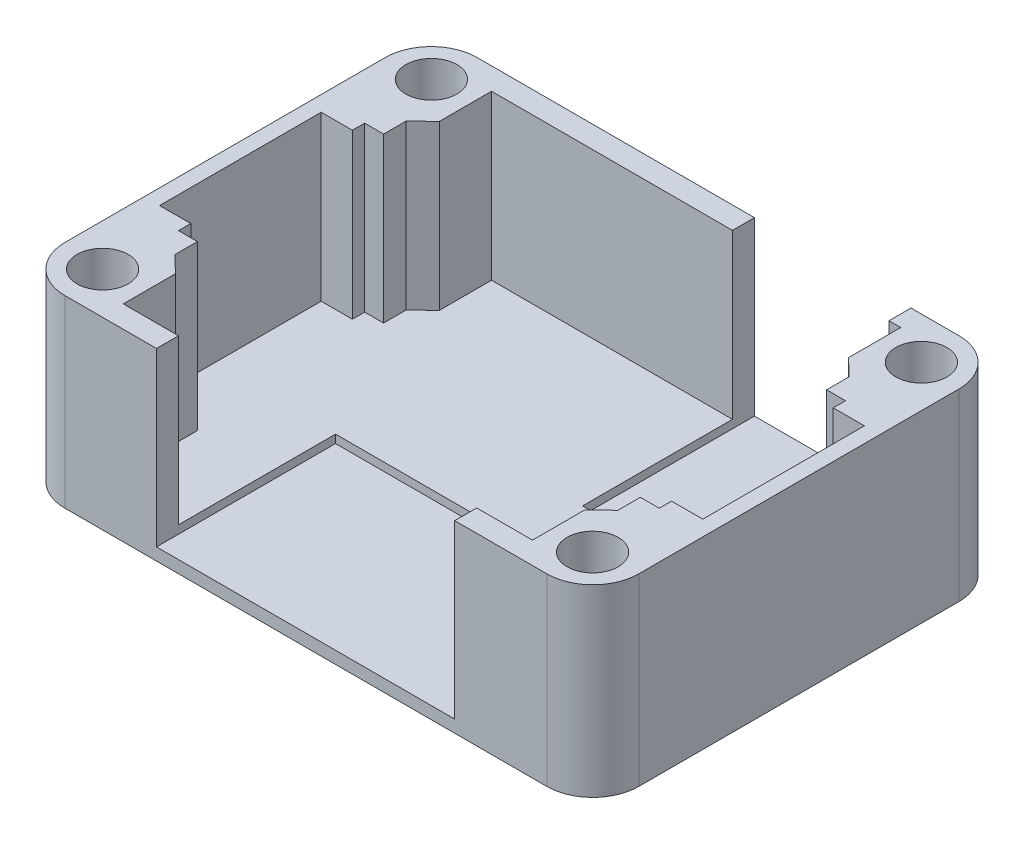
SolidWorks part; units mm, degrees
ref_plane "Front Plane" through (0, 0, 0) normal (0, 0, 1) x (1, 0, 0)
ref_plane "Top Plane" through (0, 0, 0) normal (0, 1, 0) x (1, 0, 0)
ref_plane "Right Plane" through (0, 0, 0) normal (1, 0, 0) x (0, 0, -1)
sketch "Sketch1" plane through (0, 0, 0) normal (0, 1, 0) x (1, 0, 0)
  line L1 (-20, -18) -> (20, -18)
  line L3 (-20, 18) -> (20, 18)
  line L5 (-20, -18) -> (20, 18) construction
  line L6 (-20, 18) -> (20, -18) construction
  line L9 (-20, -12.9) -> (-21.65, -11.3)
  line L16 (-20, -18) -> (-20, -12.9)
  line L17 (-21.65, -11.3) -> (-21.65, -9.1)
  line L18 (-21.65, -9.1) -> (-23.5, -9.1)
  line L19 (-23.5, -9.1) -> (-23.5, -7.9)
  line L20 (-23.5, -7.9) -> (-26.55, -7.9)
  line L21 (-26.55, -7.9) -> (-26.55, 7.9)
  line L22 (-55, 0) -> (55, 0) construction
  line L23 (-23.5, 7.9) -> (-26.55, 7.9)
  line L24 (-23.5, 9.1) -> (-23.5, 7.9)
  line L25 (-21.65, 9.1) -> (-23.5, 9.1)
  line L26 (-21.65, 11.3) -> (-21.65, 9.1)
  line L27 (-20, 12.9) -> (-21.65, 11.3)
  line L28 (-20, 18) -> (-20, 12.9)
  line L29 (0, -55) -> (0, 55) construction
  line L30 (20, 18) -> (20, 12.9)
  line L31 (20, 12.9) -> (21.65, 11.3)
  line L32 (21.65, 11.3) -> (21.65, 9.1)
  line L33 (21.65, 9.1) -> (23.5, 9.1)
  line L34 (23.5, 9.1) -> (23.5, 7.9)
  line L35 (23.5, 7.9) -> (26.55, 7.9)
  line L36 (26.55, -7.9) -> (26.55, 7.9)
  line L37 (23.5, -7.9) -> (26.55, -7.9)
  line L38 (23.5, -9.1) -> (23.5, -7.9)
  line L39 (21.65, -9.1) -> (23.5, -9.1)
  line L40 (21.65, -11.3) -> (21.65, -9.1)
  line L41 (20, -18) -> (20, -12.9)
  line L42 (20, -12.9) -> (21.65, -11.3)
  line L43 (0, 28.0577) -> (0, -22.6884) construction
  line L44 (23.55, 20.15) -> (-23.55, 20.15)
  line L45 (28.05, 15.65) -> (28.05, -15.65)
  line L46 (23.55, -20.15) -> (-23.55, -20.15)
  line L47 (-28.05, 15.65) -> (-28.05, -15.65)
  line L48 (28.05, 20.15) -> (-28.05, -20.15) construction
  line L49 (28.05, -20.15) -> (-28.05, 20.15) construction
  arc A0 (-23.55, 20.15) -> (-28.05, 15.65) centre (-23.55, 15.65) ccw
  arc A1 (23.55, 20.15) -> (28.05, 15.65) centre (23.55, 15.65) cw
  arc A2 (28.05, -15.65) -> (23.55, -20.15) centre (23.55, -15.65) cw
  arc A3 (-23.55, -20.15) -> (-28.05, -15.65) centre (-23.55, -15.65) cw
  point P0 (0, 0)
  point P10 (0, 0)
  point P17 (-26.55, 0)
  point P36 (25.8, 0)
  point P53 (0, 0)
  point P54 (0, 0)
  point P55 (0, 28.0577)
  point P56 (0, 0)
  dimension "D12" = 4.5
  dimension "D1" = 5.1
  dimension "D2" = 40
  dimension "D3" = 36
  dimension "D4" = 15.8
  dimension "D5" = 18.2
  dimension "D6" = 22.6
  dimension "D7" = 1.5
  dimension "D8" = 47
  dimension "D9" = 43.3
  dimension "D10" = 56.1
  dimension "D11" = 40.3
  dimension "D13" = 1.5
extrude "Boss-Extrude1" add sketch "Sketch1" along normal blind 16
sketch "Sketch2" plane through (0, 0, 0) normal (0, -1, 0) x (1, 0, 0)
  line L4 (-23.55, -20.15) -> (23.55, -20.15)
  line L5 (28.05, -15.65) -> (28.05, 15.65)
  line L6 (23.55, 20.15) -> (-23.55, 20.15)
  line L7 (-28.05, 15.65) -> (-28.05, -15.65)
  line L8 (-23.55, -20.15) -> (23.55, -20.15)
  line L9 (28.05, -15.65) -> (28.05, 15.65)
  line L10 (23.55, 20.15) -> (-23.55, 20.15)
  line L11 (-28.05, 15.65) -> (-28.05, -15.65)
  arc A4 (-28.05, -15.65) -> (-23.55, -20.15) centre (-23.55, -15.65) ccw
  arc A5 (23.55, -20.15) -> (28.05, -15.65) centre (23.55, -15.65) ccw
  arc A6 (28.05, 15.65) -> (23.55, 20.15) centre (23.55, 15.65) ccw
  arc A7 (-23.55, 20.15) -> (-28.05, 15.65) centre (-23.55, 15.65) ccw
  arc A8 (-28.05, -15.65) -> (-23.55, -20.15) centre (-23.55, -15.65) ccw
  arc A9 (23.55, -20.15) -> (28.05, -15.65) centre (23.55, -15.65) ccw
  arc A10 (28.05, 15.65) -> (23.55, 20.15) centre (23.55, 15.65) ccw
  arc A11 (-23.55, 20.15) -> (-28.05, 15.65) centre (-23.55, 15.65) ccw
  dimension "D1" = 0
extrude "Boss-Extrude2" add sketch "Sketch2" along normal blind 2
sketch "Sketch3" plane through (0, 0, -20.15) normal (0, 0, -1) x (-1, 0, 0)
  line L0 (-23.55, 16) -> (23.55, 16) construction
  line L1 (-18.85, 16) -> (-3.55, 16)
  line L2 (-18.85, 16) -> (-18.85, -0.8)
  line L3 (-18.85, -0.8) -> (-3.55, -0.8)
  line L4 (-3.55, 16) -> (-3.55, -0.8)
  line L6 (28.05, 16) -> (28.05, -2) construction
  point P11 (-4.6086, 20)
  dimension "D1" = 31.6
  dimension "D2" = 15.3
  dimension "D3" = 16.8
extrude "Cut-Extrude1" cut sketch "Sketch3" against normal blind 16.8
sketch "Sketch4" plane through (0, 16, 0) normal (0, 1, 0) x (1, 0, 0)
  line L1 (28.05, -15.65) -> (28.05, 15.65) construction
  line L2 (-37.0205, 0) -> (37.0205, 0) construction
  line L3 (0, 24.1968) -> (0, -24.1968) construction
  circle A0 centre (23.95, 16.0696) radius 2.5
  circle A1 centre (23.95, -16.0696) radius 2.5
  circle A2 centre (-23.95, 16.0696) radius 2.5
  circle A3 centre (-23.95, -16.0696) radius 2.5
  point P3 (-7.7174, -24.1968)
  point P7 (0, 0)
  point P13 (0, 0)
  dimension "D1" = 5
  dimension "D2" = 4.1
  dimension "D3" = 4.1
extrude "Cut-Extrude2" cut sketch "Sketch4" against normal through all
sketch "Sketch5" plane through (0, 0, 20.15) normal (0, 0, 1) x (1, 0, 0)
  line L0 (28.05, 16) -> (28.05, -2) construction
  line L16 (-23.55, 16) -> (23.55, 16) construction
  line L17 (-14.6, 16) -> (14.55, 16)
  line L18 (-14.6, 16) -> (-14.6, -0.8)
  line L19 (-14.6, -0.8) -> (14.55, -0.8)
  line L20 (14.55, 16) -> (14.55, -0.8)
  point P11 (-16.3924, 20)
  dimension "D1" = 16.8
  dimension "D2" = 29.15
  dimension "D3" = 13.5
extrude "Cut-Extrude3" cut sketch "Sketch5" against normal blind 17.5
sketch "Sketch6" plane through (0, -2, 0) normal (0, -1, 0) x (1, 0, 0)
  line L1 (19.77, -11.19) -> (-1.55, -11.19)
  line L2 (19.77, -11.19) -> (19.77, -17.27)
  line L3 (19.77, -17.27) -> (-1.55, -17.27)
  line L4 (-1.55, -11.19) -> (-1.55, -17.27)
  point P4 (-1.55, -14.23)
  dimension "D1" = 19.77
  dimension "D2" = 21.32
  dimension "D3" = 6.08
  dimension "D4" = 14.23
